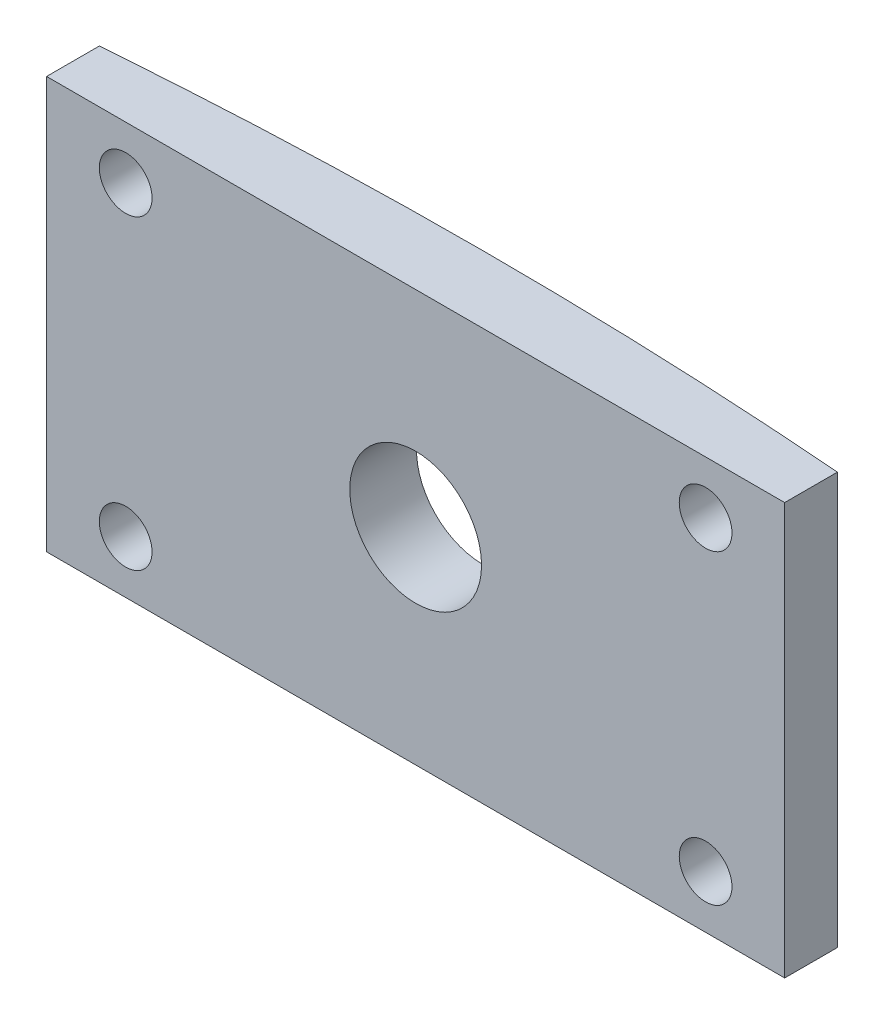
SolidWorks part; units mm, degrees
ref_plane "Front Plane" through (0, 0, 0) normal (0, 0, 1) x (1, 0, 0)
ref_plane "Top Plane" through (0, 0, 0) normal (0, 1, 0) x (1, 0, 0)
ref_plane "Right Plane" through (0, 0, 0) normal (1, 0, 0) x (0, 0, -1)
sketch "Sketch1" plane through (0, 0, 0) normal (0, 1, 0) x (1, 0, 0)
  line L0 (-236.1635, 0) -> (254.1119, 0) construction
  line L1 (-140, 0) -> (-140, -20)
  line L2 (-140, -20) -> (140, -20)
  line L3 (140, -20) -> (140, 0)
  arc A1 (-140, 0) -> (140, 0) centre (0, -1770.674) cw
  dimension "D5" = 1776.2
  dimension "D1" = 140
  dimension "D2" = 140
  dimension "D4" = 20
extrude "Boss-Extrude1" add sketch "Sketch1" along normal blind 156.2
sketch "Sketch2" plane through (0, 0, 20) normal (0, 0, 1) x (1, 0, 0)
  line L0 (-140, 156.2) -> (-140, 0) construction
  line L1 (-140, 0) -> (140, 0) construction
  line L2 (-140, 156.2) -> (140, 156.2) construction
  line L3 (0, -55) -> (0, 55) construction
  circle A0 centre (-110, 136.2) radius 10
  circle A1 centre (-110, 20) radius 10
  circle A2 centre (110, 20) radius 10
  circle A3 centre (110, 136.2) radius 10
  circle A4 centre (0, 78.1) radius 25
  dimension "D1" = 20
  dimension "D2" = 20
  dimension "D7" = 50
  dimension "D3" = 30
  dimension "D4" = 20
  dimension "D5" = 20
  dimension "D6" = 30
  dimension "D8" = 78.1
extrude "Cut-Extrude1" cut sketch "Sketch2" against normal through all
